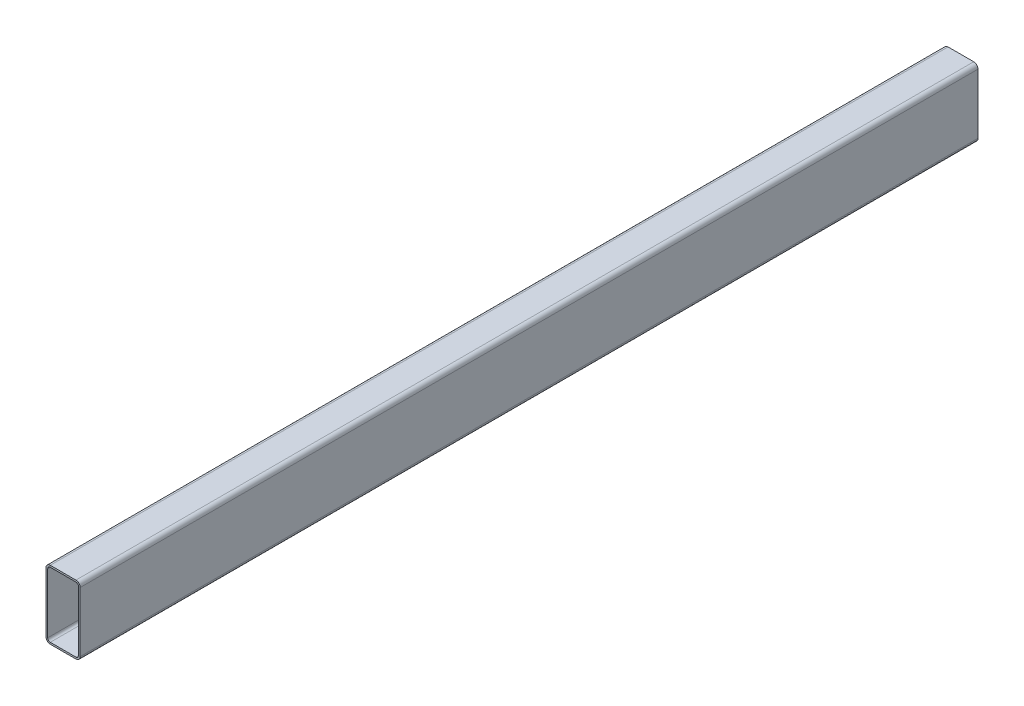
SolidWorks part; units mm, degrees
ref_plane "Front Plane" through (0, 0, 0) normal (0, 0, 1) x (1, 0, 0)
ref_plane "Top Plane" through (0, 0, 0) normal (0, 1, 0) x (1, 0, 0)
ref_plane "Right Plane" through (0, 0, 0) normal (1, 0, 0) x (0, 0, -1)
sketch "Sketch1" plane through (0, 0, 0) normal (0, 0, 1) x (1, 0, 0)
  line L0 (-18, -35) -> (-18, 35)
  line L1 (-15, -40) -> (15, -40)
  line L2 (-20, -35) -> (-20, 35)
  line L3 (-15, 40) -> (15, 40)
  line L4 (20, -35) -> (20, 35)
  line L5 (-20, -40) -> (20, 40) construction
  line L6 (-20, 40) -> (20, -40) construction
  line L7 (-15, 38) -> (15, 38)
  line L8 (18, -35) -> (18, 35)
  line L9 (-15, -38) -> (15, -38)
  arc A0 (15, -40) -> (20, -35) centre (15, -35) ccw
  arc A1 (-15, -40) -> (-20, -35) centre (-15, -35) cw
  arc A2 (15, 40) -> (20, 35) centre (15, 35) cw
  arc A3 (-20, 35) -> (-15, 40) centre (-15, 35) cw
  arc A4 (-18, 35) -> (-15, 38) centre (-15, 35) cw
  arc A5 (15, 38) -> (18, 35) centre (15, 35) cw
  arc A6 (15, -38) -> (18, -35) centre (15, -35) ccw
  arc A7 (-15, -38) -> (-18, -35) centre (-15, -35) cw
  point P0 (0, 0)
  dimension "D3" = 5
  dimension "D1" = 80
  dimension "D2" = 40
  dimension "D4" = 2
extrude "Boss-Extrude1" add sketch "Sketch1" along normal blind 1050
equation "\"tube height\"= \"D1@Sketch1\""
equation "\"tube width\"= \"D2@Sketch1\""
equation "\"tube thickness\"= \"D4@Sketch1\""
equation "\"tube radius\"= \"D4@Sketch1\""
equation "\"tubelenght\"=1050"
equation "\"D1@Boss-Extrude1\"=\"tubelenght\""
